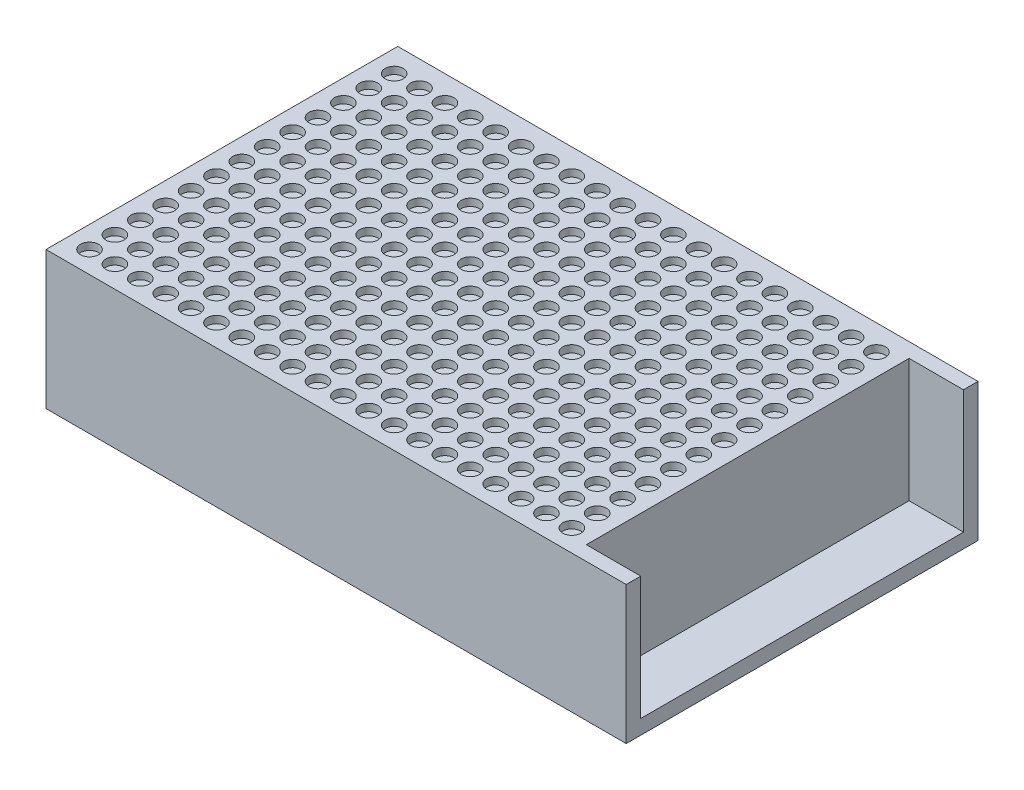
SolidWorks part; units mm, degrees
material "Простая углеродистая сталь"
ref_plane "Спереди" through (0, 0, 0) normal (0, 0, 1) x (1, 0, 0)
ref_plane "Сверху" through (0, 0, 0) normal (0, 1, 0) x (1, 0, 0)
ref_plane "Справа" through (0, 0, 0) normal (1, 0, 0) x (0, 0, -1)
sketch "Эскиз1" plane through (0, 0, 0) normal (0, 1, 0) x (1, 0, 0)
  line L0 (0, 0) -> (160, 0)
  line L1 (0, 0) -> (0, 97)
  line L2 (160, 0) -> (160, 97)
  line L3 (0, 97) -> (160, 97)
  dimension "D1" = 97
  dimension "D2" = 160
extrude "Бобышка-Вытянуть1" add sketch "Эскиз1" along normal blind 38
sketch "Эскиз2" plane through (0, 38, 0) normal (0, 1, 0) x (1, 0, 0)
  line L0 (160, 4) -> (145, 4)
  line L1 (160, 4) -> (160, 93)
  line L2 (145, 4) -> (145, 93)
  line L3 (160, 93) -> (145, 93)
  line L4 (160, 0) -> (160, 97) construction
  line L5 (0, 0) -> (160, 0) construction
  line L6 (160, 97) -> (0, 97) construction
  dimension "D1" = 15
  dimension "D2" = 4
  dimension "D3" = 4
extrude "Вырез-Вытянуть1" cut sketch "Эскиз2" against normal blind 34
sketch "Эскиз3" plane through (0, 38, 0) normal (0, 1, 0) x (1, 0, 0)
  line L0 (4, 4) -> (4, 93) construction
  line L1 (4, 4) -> (141, 4) construction
  line L2 (4, 93) -> (141, 93) construction
  line L3 (141, 4) -> (141, 93) construction
  line L4 (145, 4) -> (160, 4) construction
  line L5 (160, 93) -> (145, 93) construction
  line L6 (0, 97) -> (0, 0) construction
  line L7 (145, 93) -> (145, 4) construction
  line L8 (6, 4) -> (6, 93) construction
  line L9 (6, 6) -> (141, 6) construction
  circle A0 centre (6, 6) radius 2.5
  circle A1 centre (13, 6) radius 2.5
  circle A2 centre (20, 6) radius 2.5
  circle A3 centre (27, 6) radius 2.5
  circle A4 centre (34, 6) radius 2.5
  circle A5 centre (41, 6) radius 2.5
  circle A6 centre (48, 6) radius 2.5
  circle A7 centre (55, 6) radius 2.5
  circle A8 centre (62, 6) radius 2.5
  circle A9 centre (69, 6) radius 2.5
  circle A10 centre (76, 6) radius 2.5
  circle A11 centre (83, 6) radius 2.5
  circle A12 centre (90, 6) radius 2.5
  circle A13 centre (97, 6) radius 2.5
  circle A14 centre (104, 6) radius 2.5
  circle A15 centre (111, 6) radius 2.5
  circle A16 centre (118, 6) radius 2.5
  circle A17 centre (125, 6) radius 2.5
  circle A18 centre (132, 6) radius 2.5
  circle A19 centre (139, 6) radius 2.5
  circle A20 centre (13, 13) radius 2.5
  circle A21 centre (20, 13) radius 2.5
  circle A22 centre (27, 13) radius 2.5
  circle A23 centre (34, 13) radius 2.5
  circle A24 centre (41, 13) radius 2.5
  circle A25 centre (48, 13) radius 2.5
  circle A26 centre (55, 13) radius 2.5
  circle A27 centre (62, 13) radius 2.5
  circle A28 centre (69, 13) radius 2.5
  circle A29 centre (76, 13) radius 2.5
  circle A30 centre (83, 13) radius 2.5
  circle A31 centre (90, 13) radius 2.5
  circle A32 centre (97, 13) radius 2.5
  circle A33 centre (104, 13) radius 2.5
  circle A34 centre (111, 13) radius 2.5
  circle A35 centre (118, 13) radius 2.5
  circle A36 centre (125, 13) radius 2.5
  circle A37 centre (132, 13) radius 2.5
  circle A38 centre (139, 13) radius 2.5
  circle A39 centre (13, 20) radius 2.5
  circle A40 centre (20, 20) radius 2.5
  circle A41 centre (27, 20) radius 2.5
  circle A42 centre (34, 20) radius 2.5
  circle A43 centre (41, 20) radius 2.5
  circle A44 centre (48, 20) radius 2.5
  circle A45 centre (55, 20) radius 2.5
  circle A46 centre (62, 20) radius 2.5
  circle A47 centre (69, 20) radius 2.5
  circle A48 centre (76, 20) radius 2.5
  circle A49 centre (83, 20) radius 2.5
  circle A50 centre (90, 20) radius 2.5
  circle A51 centre (97, 20) radius 2.5
  circle A52 centre (104, 20) radius 2.5
  circle A53 centre (111, 20) radius 2.5
  circle A54 centre (118, 20) radius 2.5
  circle A55 centre (125, 20) radius 2.5
  circle A56 centre (132, 20) radius 2.5
  circle A57 centre (139, 20) radius 2.5
  circle A58 centre (13, 27) radius 2.5
  circle A59 centre (20, 27) radius 2.5
  circle A60 centre (27, 27) radius 2.5
  circle A61 centre (34, 27) radius 2.5
  circle A62 centre (41, 27) radius 2.5
  circle A63 centre (48, 27) radius 2.5
  circle A64 centre (55, 27) radius 2.5
  circle A65 centre (62, 27) radius 2.5
  circle A66 centre (69, 27) radius 2.5
  circle A67 centre (76, 27) radius 2.5
  circle A68 centre (83, 27) radius 2.5
  circle A69 centre (90, 27) radius 2.5
  circle A70 centre (97, 27) radius 2.5
  circle A71 centre (104, 27) radius 2.5
  circle A72 centre (111, 27) radius 2.5
  circle A73 centre (118, 27) radius 2.5
  circle A74 centre (125, 27) radius 2.5
  circle A75 centre (132, 27) radius 2.5
  circle A76 centre (139, 27) radius 2.5
  circle A77 centre (13, 34) radius 2.5
  circle A78 centre (20, 34) radius 2.5
  circle A79 centre (27, 34) radius 2.5
  circle A80 centre (34, 34) radius 2.5
  circle A81 centre (41, 34) radius 2.5
  circle A82 centre (48, 34) radius 2.5
  circle A83 centre (55, 34) radius 2.5
  circle A84 centre (62, 34) radius 2.5
  circle A85 centre (69, 34) radius 2.5
  circle A86 centre (76, 34) radius 2.5
  circle A87 centre (83, 34) radius 2.5
  circle A88 centre (90, 34) radius 2.5
  circle A89 centre (97, 34) radius 2.5
  circle A90 centre (104, 34) radius 2.5
  circle A91 centre (111, 34) radius 2.5
  circle A92 centre (118, 34) radius 2.5
  circle A93 centre (125, 34) radius 2.5
  circle A94 centre (132, 34) radius 2.5
  circle A95 centre (139, 34) radius 2.5
  circle A96 centre (13, 41) radius 2.5
  circle A97 centre (20, 41) radius 2.5
  circle A98 centre (27, 41) radius 2.5
  circle A99 centre (34, 41) radius 2.5
  circle A100 centre (41, 41) radius 2.5
  circle A101 centre (48, 41) radius 2.5
  circle A102 centre (55, 41) radius 2.5
  circle A103 centre (62, 41) radius 2.5
  circle A104 centre (69, 41) radius 2.5
  circle A105 centre (76, 41) radius 2.5
  circle A106 centre (83, 41) radius 2.5
  circle A107 centre (90, 41) radius 2.5
  circle A108 centre (97, 41) radius 2.5
  circle A109 centre (104, 41) radius 2.5
  circle A110 centre (111, 41) radius 2.5
  circle A111 centre (118, 41) radius 2.5
  circle A112 centre (125, 41) radius 2.5
  circle A113 centre (132, 41) radius 2.5
  circle A114 centre (139, 41) radius 2.5
  circle A115 centre (13, 48) radius 2.5
  circle A116 centre (20, 48) radius 2.5
  circle A117 centre (27, 48) radius 2.5
  circle A118 centre (34, 48) radius 2.5
  circle A119 centre (41, 48) radius 2.5
  circle A120 centre (48, 48) radius 2.5
  circle A121 centre (55, 48) radius 2.5
  circle A122 centre (62, 48) radius 2.5
  circle A123 centre (69, 48) radius 2.5
  circle A124 centre (76, 48) radius 2.5
  circle A125 centre (83, 48) radius 2.5
  circle A126 centre (90, 48) radius 2.5
  circle A127 centre (97, 48) radius 2.5
  circle A128 centre (104, 48) radius 2.5
  circle A129 centre (111, 48) radius 2.5
  circle A130 centre (118, 48) radius 2.5
  circle A131 centre (125, 48) radius 2.5
  circle A132 centre (132, 48) radius 2.5
  circle A133 centre (139, 48) radius 2.5
  circle A134 centre (13, 55) radius 2.5
  circle A135 centre (20, 55) radius 2.5
  circle A136 centre (27, 55) radius 2.5
  circle A137 centre (34, 55) radius 2.5
  circle A138 centre (41, 55) radius 2.5
  circle A139 centre (48, 55) radius 2.5
  circle A140 centre (55, 55) radius 2.5
  circle A141 centre (62, 55) radius 2.5
  circle A142 centre (69, 55) radius 2.5
  circle A143 centre (76, 55) radius 2.5
  circle A144 centre (83, 55) radius 2.5
  circle A145 centre (90, 55) radius 2.5
  circle A146 centre (97, 55) radius 2.5
  circle A147 centre (104, 55) radius 2.5
  circle A148 centre (111, 55) radius 2.5
  circle A149 centre (118, 55) radius 2.5
  circle A150 centre (125, 55) radius 2.5
  circle A151 centre (132, 55) radius 2.5
  circle A152 centre (139, 55) radius 2.5
  circle A153 centre (13, 62) radius 2.5
  circle A154 centre (20, 62) radius 2.5
  circle A155 centre (27, 62) radius 2.5
  circle A156 centre (34, 62) radius 2.5
  circle A157 centre (41, 62) radius 2.5
  circle A158 centre (48, 62) radius 2.5
  circle A159 centre (55, 62) radius 2.5
  circle A160 centre (62, 62) radius 2.5
  circle A161 centre (69, 62) radius 2.5
  circle A162 centre (76, 62) radius 2.5
  circle A163 centre (83, 62) radius 2.5
  circle A164 centre (90, 62) radius 2.5
  circle A165 centre (97, 62) radius 2.5
  circle A166 centre (104, 62) radius 2.5
  circle A167 centre (111, 62) radius 2.5
  circle A168 centre (118, 62) radius 2.5
  circle A169 centre (125, 62) radius 2.5
  circle A170 centre (132, 62) radius 2.5
  circle A171 centre (139, 62) radius 2.5
  circle A172 centre (13, 69) radius 2.5
  circle A173 centre (20, 69) radius 2.5
  circle A174 centre (27, 69) radius 2.5
  circle A175 centre (34, 69) radius 2.5
  circle A176 centre (41, 69) radius 2.5
  circle A177 centre (48, 69) radius 2.5
  circle A178 centre (55, 69) radius 2.5
  circle A179 centre (62, 69) radius 2.5
  circle A180 centre (69, 69) radius 2.5
  circle A181 centre (76, 69) radius 2.5
  circle A182 centre (83, 69) radius 2.5
  circle A183 centre (90, 69) radius 2.5
  circle A184 centre (97, 69) radius 2.5
  circle A185 centre (104, 69) radius 2.5
  circle A186 centre (111, 69) radius 2.5
  circle A187 centre (118, 69) radius 2.5
  circle A188 centre (125, 69) radius 2.5
  circle A189 centre (132, 69) radius 2.5
  circle A190 centre (139, 69) radius 2.5
  circle A191 centre (13, 76) radius 2.5
  circle A192 centre (20, 76) radius 2.5
  circle A193 centre (27, 76) radius 2.5
  circle A194 centre (34, 76) radius 2.5
  circle A195 centre (41, 76) radius 2.5
  circle A196 centre (48, 76) radius 2.5
  circle A197 centre (55, 76) radius 2.5
  circle A198 centre (62, 76) radius 2.5
  circle A199 centre (69, 76) radius 2.5
  circle A200 centre (76, 76) radius 2.5
  circle A201 centre (83, 76) radius 2.5
  circle A202 centre (90, 76) radius 2.5
  circle A203 centre (97, 76) radius 2.5
  circle A204 centre (104, 76) radius 2.5
  circle A205 centre (111, 76) radius 2.5
  circle A206 centre (118, 76) radius 2.5
  circle A207 centre (125, 76) radius 2.5
  circle A208 centre (132, 76) radius 2.5
  circle A209 centre (139, 76) radius 2.5
  circle A210 centre (13, 83) radius 2.5
  circle A211 centre (20, 83) radius 2.5
  circle A212 centre (27, 83) radius 2.5
  circle A213 centre (34, 83) radius 2.5
  circle A214 centre (41, 83) radius 2.5
  circle A215 centre (48, 83) radius 2.5
  circle A216 centre (55, 83) radius 2.5
  circle A217 centre (62, 83) radius 2.5
  circle A218 centre (69, 83) radius 2.5
  circle A219 centre (76, 83) radius 2.5
  circle A220 centre (83, 83) radius 2.5
  circle A221 centre (90, 83) radius 2.5
  circle A222 centre (97, 83) radius 2.5
  circle A223 centre (104, 83) radius 2.5
  circle A224 centre (111, 83) radius 2.5
  circle A225 centre (118, 83) radius 2.5
  circle A226 centre (125, 83) radius 2.5
  circle A227 centre (132, 83) radius 2.5
  circle A228 centre (139, 83) radius 2.5
  circle A229 centre (13, 90) radius 2.5
  circle A230 centre (20, 90) radius 2.5
  circle A231 centre (27, 90) radius 2.5
  circle A232 centre (34, 90) radius 2.5
  circle A233 centre (41, 90) radius 2.5
  circle A234 centre (48, 90) radius 2.5
  circle A235 centre (55, 90) radius 2.5
  circle A236 centre (62, 90) radius 2.5
  circle A237 centre (69, 90) radius 2.5
  circle A238 centre (76, 90) radius 2.5
  circle A239 centre (83, 90) radius 2.5
  circle A240 centre (90, 90) radius 2.5
  circle A241 centre (97, 90) radius 2.5
  circle A242 centre (104, 90) radius 2.5
  circle A243 centre (111, 90) radius 2.5
  circle A244 centre (118, 90) radius 2.5
  circle A245 centre (125, 90) radius 2.5
  circle A246 centre (132, 90) radius 2.5
  circle A247 centre (139, 90) radius 2.5
  circle A248 centre (6, 13) radius 2.5
  circle A249 centre (6, 20) radius 2.5
  circle A250 centre (6, 27) radius 2.5
  circle A251 centre (6, 34) radius 2.5
  circle A252 centre (6, 41) radius 2.5
  circle A253 centre (6, 48) radius 2.5
  circle A254 centre (6, 55) radius 2.5
  circle A255 centre (6, 62) radius 2.5
  circle A256 centre (6, 69) radius 2.5
  circle A257 centre (6, 76) radius 2.5
  circle A258 centre (6, 83) radius 2.5
  circle A259 centre (6, 90) radius 2.5
  dimension "D3" = 5
  dimension "D4" = 2
  dimension "D8" = 7
  dimension "D9" = 7
  dimension "D1" = 4
  dimension "D2" = 4
  dimension "D5" = 2
  dimension "D6" = 20
  dimension "D7" = 13
extrude "Вырез-Вытянуть2" cut sketch "Эскиз3" against normal blind 2
